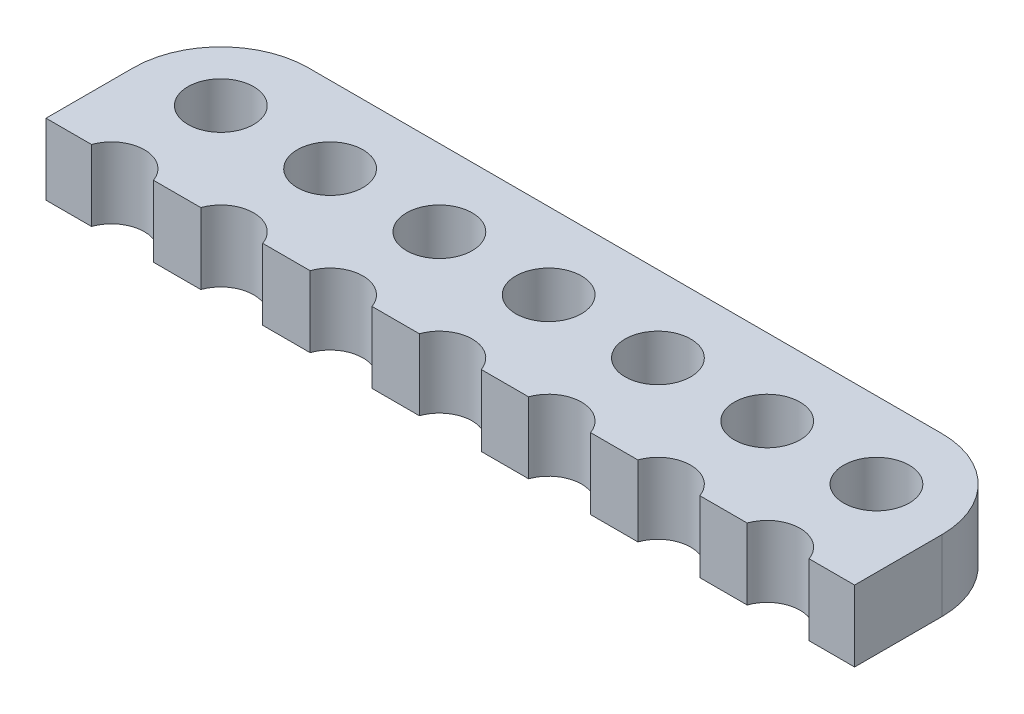
SolidWorks part; units mm, degrees
material "ABS"
ref_plane "Front Plane" through (0, 0, 0) normal (0, 0, 1) x (1, 0, 0)
ref_plane "Top Plane" through (0, 0, 0) normal (0, 1, 0) x (1, 0, 0)
ref_plane "Right Plane" through (0, 0, 0) normal (1, 0, 0) x (0, 0, -1)
sketch "Sketch1" plane through (0, 0, 0) normal (0, 1, 0) x (1, 0, 0)
  line L0 (-18.5, 4) -> (18.5, -4) construction
  line L1 (-14.5, 4) -> (14.5, 4)
  line L2 (-18.5, 0) -> (-18.5, -4)
  line L3 (-18.5, -4) -> (-16.4169, -4)
  line L4 (18.5, 0) -> (18.5, -4)
  line L5 (16.4169, -4) -> (18.5, -4)
  line L6 (11.4169, -4) -> (13.5831, -4)
  line L7 (6.4169, -4) -> (8.5831, -4)
  line L8 (1.4169, -4) -> (3.5831, -4)
  line L9 (-3.5831, -4) -> (-1.4169, -4)
  line L10 (-8.5831, -4) -> (-6.4169, -4)
  line L11 (-13.5831, -4) -> (-11.4169, -4)
  circle A0 centre (-15, 0.5) radius 1.5025
  arc A1 (14.5, 4) -> (18.5, 0) centre (14.5, 0) cw
  arc A2 (-14.5, 4) -> (-18.5, 0) centre (-14.5, 0) ccw
  circle A3 centre (-10, 0.5) radius 1.5025
  circle A4 centre (-5, 0.5) radius 1.5025
  circle A5 centre (0, 0.5) radius 1.5025
  circle A6 centre (5, 0.5) radius 1.5025
  circle A7 centre (10, 0.5) radius 1.5025
  circle A8 centre (15, 0.5) radius 1.5025
  arc A9 (-8.5831, -4) -> (-11.4169, -4) centre (-10, -4.5) ccw
  arc A10 (-3.5831, -4) -> (-6.4169, -4) centre (-5, -4.5) ccw
  arc A11 (1.4169, -4) -> (-1.4169, -4) centre (0, -4.5) ccw
  arc A12 (6.4169, -4) -> (3.5831, -4) centre (5, -4.5) ccw
  arc A13 (11.4169, -4) -> (8.5831, -4) centre (10, -4.5) ccw
  arc A14 (16.4169, -4) -> (13.5831, -4) centre (15, -4.5) ccw
  arc A15 (-13.5831, -4) -> (-16.4169, -4) centre (-15, -4.5) ccw
  point P9 (18.5, 4)
  dimension "D5" = 4
  dimension "D3" = 3.005
  dimension "D4" = 3.5
  dimension "D6" = 3.5
  dimension "D1" = 37
  dimension "D2" = 8
  dimension "D7" = 7
  dimension "D8" = 2
extrude "Boss-Extrude1" add sketch "Sketch1" along normal blind 3.25
